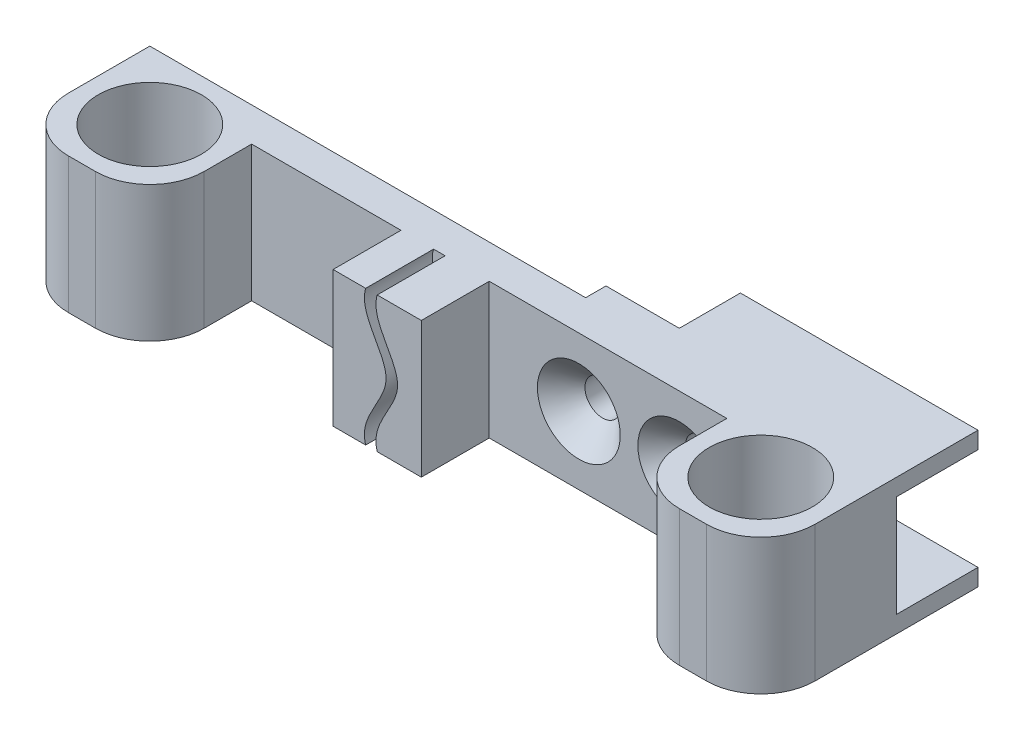
SolidWorks part; units mm, degrees
ref_plane "Plan de face" through (0, 0, 0) normal (0, 0, 1) x (1, 0, 0)
ref_plane "Plan de dessus" through (0, 0, 0) normal (0, 1, 0) x (1, 0, 0)
ref_plane "Plan de droite" through (0, 0, 0) normal (1, 0, 0) x (0, 0, -1)
sketch "Esquisse1" plane through (0, 0, 0) normal (0, 1, 0) x (1, 0, 0)
  line L0 (47, -20) -> (43, -20)
  line L1 (-55, 0) -> (55, 0)
  line L4 (55, 0) -> (55, -12)
  line L5 (35, -12) -> (35, -5)
  line L6 (35, -5) -> (-35, -5)
  line L7 (0, 0) -> (0, -5) construction
  line L8 (-35, -12) -> (-35, -5)
  line L9 (-55, 0) -> (-55, -12)
  line L10 (-47, -20) -> (-43, -20)
  circle A0 centre (45, -10) radius 7.6
  circle A1 centre (-45, -10) radius 7.6
  arc A2 (43, -20) -> (35, -12) centre (43, -12) cw
  arc A3 (47, -20) -> (55, -12) centre (47, -12) ccw
  arc A4 (-55, -12) -> (-47, -20) centre (-47, -12) ccw
  arc A5 (-35, -12) -> (-43, -20) centre (-43, -12) cw
  point P17 (35, -20)
  point P20 (55, -20)
  point P24 (-55, -20)
  point P27 (-35, -20)
  dimension "D3" = 15.2
  dimension "D8" = 8
  dimension "D10" = 8
  dimension "D1" = 55
  dimension "D2" = 45
  dimension "D4" = 20
  dimension "D5" = 5
  dimension "D6" = 10
  dimension "D7" = 10
  dimension "D9" = 10
extrude "Boss.-Extru.1" add sketch "Esquisse1" along normal blind 20
sketch "Esquisse8" plane through (0, 0, 0) normal (0, 0, -1) x (-1, 0, 0)
  line L0 (-55, 0) -> (55, 0) construction
  line L1 (-9.2, 0) -> (-32, 0)
  line L2 (-9.2, 0) -> (-9.2, 20)
  line L3 (-9.2, 20) -> (-32, 20)
  line L4 (-32, 0) -> (-32, 20)
  line L5 (-55, 20) -> (55, 20) construction
  line L6 (-55, 20) -> (-55, 0) construction
  dimension "D2" = 22.8
  dimension "D1" = 23
extrude "Boss.-Extru.4" add sketch "Esquisse8" along normal blind 3
sketch "Esquisse2" plane through (0, 0, 0) normal (0, 0, -1) x (-1, 0, 0)
  line L1 (-55, 20) -> (-20, 20)
  line L2 (-55, 20) -> (-55, 17.5)
  line L3 (-55, 17.5) -> (-20, 17.5)
  line L4 (-20, 20) -> (-20, 17.5)
  line L5 (-55, 0) -> (-20, 0)
  line L6 (-55, 0) -> (-55, 2.5)
  line L7 (-55, 2.5) -> (-20, 2.5)
  line L8 (-20, 0) -> (-20, 2.5)
  dimension "D1" = 15
  dimension "D2" = 20
  dimension "D3" = 2.5
  dimension "D4" = 35
extrude "Boss.-Extru.2" add sketch "Esquisse2" along normal blind 12
sketch "Esquisse3" plane through (0, 0, 0) normal (0, 0, -1) x (-1, 0, 0)
  line L0 (-55, 10) -> (55, 10) construction
  line L1 (-55, 17.5) -> (-55, 2.5) construction
  line L2 (55, 20) -> (55, 0) construction
  circle A0 centre (-13.2, 10) radius 2.6
  circle A1 centre (-28, 10) radius 2.6
  dimension "D1" = 5.2
  dimension "D2" = 5.2
  dimension "D3" = 14.8
  dimension "D4" = 27
extrude "Enlèv. mat.-Extru.1" cut sketch "Esquisse3" against normal blind 22 and the other way blind 3
chamfer "Chanfrein1" distance 3.5 angle 45 2 edges at (25.4, 10, 5) (10.6, 10, 5)
sketch "Esquisse4" plane through (0, 0, 0) normal (1, 0, 0) x (0, 0, -1)
  line L1 (-5, 20) -> (-15, 20)
  line L2 (-5, 20) -> (-5, 0)
  line L3 (-5, 0) -> (-15, 0)
  line L4 (-15, 20) -> (-15, 0)
  dimension "D1" = 10
extrude "Boss.-Extru.3" add sketch "Esquisse4" against normal blind 13
sketch "Esquisse7" plane through (0, 0, 15) normal (0, 0, 1) x (1, 0, 0)
  line L0 (-13, 20) -> (0, 20) construction
  line L1 (-13, 0) -> (0, 0) construction
  line L2 (0, 10) -> (-13, 10) construction
  line L3 (0, 0) -> (0, 20) construction
  line L4 (-13, 0) -> (-13, 20) construction
  line L5 (0, 20) -> (0, 0) construction
  line L6 (-8.2, 20) -> (-6.5, 20)
  line L7 (-6.5, 0) -> (-8.2, 0)
  spline S0 degree 3 poles (-6.5, 20) (-7.6022, 16.3662) (0.6022, 10) (-7.6022, 3.6338) (-6.5, 0) knots 0 0 0 0 0.5 1 1 1 1
  spline S1 degree 3 poles (-8.2, 20) (-9.3022, 16.3662) (-1.0978, 10) (-9.3022, 3.6338) (-8.2, 0) knots 0 0 0 0 0.5 1 1 1 1
  dimension "D1" = 1.7
  dimension "D2" = 1.7
  dimension "D3" = 1.7
  dimension "D4" = 1.7
  dimension "D5" = 1.7
  dimension "D6" = 6
  dimension "D7" = 6
  dimension "D8" = 3.5
  dimension "D9" = 6
  dimension "D10" = 6
extrude "Enlèv. mat.-Extru.2" cut sketch "Esquisse7" against normal blind 10
equation "\"D7@Esquisse1\"=\"D6@Esquisse1\""
equation "\"D9@Esquisse1\"=\"D6@Esquisse1\""
equation "\"D3@Esquisse2\"=(\"D2@Esquisse2\"-\"D1@Esquisse2\")/2"
equation "\"D2@Esquisse3\"=\"D1@Esquisse3\""
equation "\"D3@Esquisse3\"=19-4.2"
equation "\"D3@Esquisse7\"=\"D1@Esquisse7\""
equation "\"D2@Esquisse7\"=\"D1@Esquisse7\""
equation "\"D4@Esquisse7\"=\"D1@Esquisse7\""
equation "\"D5@Esquisse7\"=\"D1@Esquisse7\""
